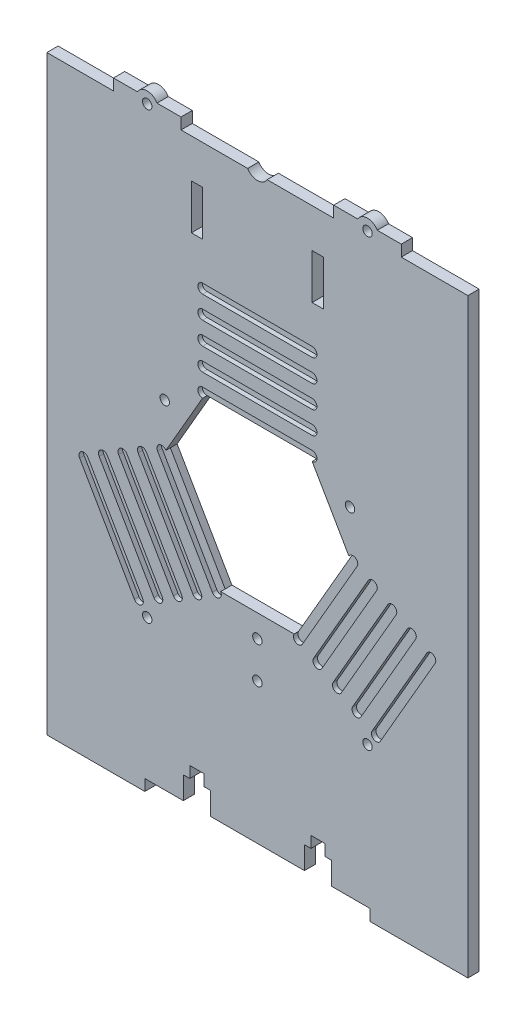
SolidWorks part; units mm, degrees
ref_plane "Front Plane" through (0, 0, 0) normal (0, 0, 1) x (1, 0, 0)
ref_plane "Top Plane" through (0, 0, 0) normal (0, 1, 0) x (1, 0, 0)
ref_plane "Right Plane" through (0, 0, 0) normal (1, 0, 0) x (0, 0, -1)
sketch "Sketch1" plane through (0, 0, 0) normal (0, 0, 1) x (1, 0, 0)
  line L1 (-93.5, 131.25) -> (93.5, 131.25)
  line L2 (-93.5, 131.25) -> (-93.5, -131.25)
  line L3 (-93.5, -131.25) -> (93.5, -131.25)
  line L4 (93.5, 131.25) -> (93.5, -131.25)
  line L5 (-93.5, 131.25) -> (93.5, -131.25) construction
  line L6 (-93.5, -131.25) -> (93.5, 131.25) construction
  point P0 (0, 0)
  dimension "D1" = 187
  dimension "D2" = 262.5
extrude "Boss-Extrude1" add sketch "Sketch1" along normal blind 5
sketch "Sketch2" plane through (0, 0, 5) normal (0, 0, 1) x (1, 0, 0)
  line L0 (-93.5, -131.25) -> (93.5, -131.25) construction
  line L1 (-50, -126.25) -> (50, -126.25)
  line L2 (-50, -126.25) -> (-50, -131.25)
  line L3 (-50, -131.25) -> (50, -131.25)
  line L4 (50, -126.25) -> (50, -131.25)
  line L5 (-50, -126.25) -> (50, -131.25) construction
  line L6 (-50, -131.25) -> (50, -126.25) construction
  line L7 (50, -126.25) -> (50, -131.25) construction
  circle A0 centre (0, 133.75) radius 5
  point P4 (0, -128.75)
extrude "Cut-Extrude1" cut sketch "Sketch2" against normal blind 5
sketch "Sketch4" plane through (0, 0, 5) normal (0, 0, 1) x (1, 0, 0)
  line L0 (48.9151, 131.25) -> (48.9151, 136.25) construction
  line L1 (93.5, 131.25) -> (4.3301, 131.25) construction
  line L2 (98, 136.25) -> (63.9151, 136.25) construction
  line L3 (0, 128.75) -> (0, 116.8054) construction
  line L4 (33.9151, 136.25) -> (44.5849, 136.25)
  line L5 (33.9151, 136.25) -> (33.9151, 131.25)
  line L6 (33.9151, 131.25) -> (63.9151, 131.25)
  line L7 (63.9151, 131.25) -> (63.9151, 136.25)
  line L8 (33.9151, 133.75) -> (63.9151, 133.75) construction
  line L9 (53.2452, 136.25) -> (63.9151, 136.25)
  line L10 (-33.9151, 133.75) -> (-63.9151, 133.75) construction
  line L11 (-48.9151, 131.25) -> (-48.9151, 136.25) construction
  line L12 (-53.2452, 136.25) -> (-63.9151, 136.25)
  line L13 (-63.9151, 131.25) -> (-63.9151, 136.25)
  line L14 (-33.9151, 131.25) -> (-63.9151, 131.25)
  line L15 (-33.9151, 136.25) -> (-33.9151, 131.25)
  line L16 (-33.9151, 136.25) -> (-44.5849, 136.25)
  arc A0 (-4.3301, 131.25) -> (4.3301, 131.25) centre (0, 133.75) ccw construction
  arc A1 (53.2452, 136.25) -> (44.5849, 136.25) centre (48.9151, 133.75) ccw
  arc A2 (-53.2452, 136.25) -> (-44.5849, 136.25) centre (-48.9151, 133.75) cw
  point P16 (48.9151, 136.25)
  point P34 (-48.9151, 136.25)
  dimension "D2" = 10
  dimension "D1" = 30
extrude "Boss-Extrude2" add sketch "Sketch4" against normal blind 5
sketch "Sketch3" plane through (0, 0, 5) normal (0, 0, 1) x (1, 0, 0)
  line L0 (0, -126.25) -> (0, -94.9289) construction
  line L1 (50, -126.25) -> (-50, -126.25) construction
  line L2 (0, -94.9289) -> (-53.8131, -94.9289) construction
  line L3 (-26.9066, -94.9289) -> (-26.9066, -126.25) construction
  line L4 (-32.9066, -126.25) -> (-32.9066, -116.25)
  line L5 (-32.9066, -116.25) -> (-30.0066, -116.25)
  line L6 (-30.0066, -116.25) -> (-30.0066, -111.25)
  line L7 (-23.8066, -116.25) -> (-23.8066, -111.25)
  line L8 (-20.9066, -116.25) -> (-23.8066, -116.25)
  line L9 (-20.9066, -126.25) -> (-20.9066, -116.25)
  line L10 (-30.0066, -111.25) -> (-23.8066, -111.25)
  line L11 (-32.9066, -126.25) -> (-20.9066, -126.25)
  line L12 (32.9066, -126.25) -> (20.9066, -126.25)
  line L13 (30.0066, -111.25) -> (23.8066, -111.25)
  line L14 (20.9066, -126.25) -> (20.9066, -116.25)
  line L15 (20.9066, -116.25) -> (23.8066, -116.25)
  line L16 (23.8066, -116.25) -> (23.8066, -111.25)
  line L17 (30.0066, -116.25) -> (30.0066, -111.25)
  line L18 (32.9066, -116.25) -> (30.0066, -116.25)
  line L19 (32.9066, -126.25) -> (32.9066, -116.25)
  line L20 (-63.9151, -63.75) -> (-33.9151, -63.75) construction
  line L21 (-63.9151, -61.25) -> (-63.9151, -66.25) construction
  line L22 (-33.9151, -61.25) -> (-33.9151, -66.25) construction
  line L23 (-15, -63.75) -> (15, -63.75) construction
  line L24 (-15, -61.25) -> (-15, -66.25) construction
  line L25 (15, -61.25) -> (15, -66.25) construction
  line L26 (33.9151, -63.75) -> (63.9151, -63.75) construction
  line L27 (33.9151, -61.25) -> (33.9151, -66.25) construction
  line L28 (63.9151, -61.25) -> (63.9151, -66.25) construction
  circle A0 centre (-48.9151, 133.75) radius 2.1
  circle A1 centre (48.9151, 133.75) radius 2.1
  circle A2 centre (-48.9151, -63.75) radius 2.1
  circle A3 centre (0, -63.75) radius 2.1
  circle A4 centre (48.9151, -63.75) radius 2.1
  dimension "D5" = 4.2
  dimension "D6" = 4.2
  dimension "D7" = 4.2
  dimension "D1" = 10
  dimension "D2" = 2.9
  dimension "D3" = 5
  dimension "D4" = 6
extrude "Cut-Extrude2" cut sketch "Sketch3" against normal blind 5
sketch "Sketch5" plane through (0, 0, 5) normal (0, 0, 1) x (1, 0, 0)
  line L0 (0, 0) -> (0, 75) construction
  line L1 (0, 0) -> (64.9519, -37.5) construction
  line L2 (0, 0) -> (-64.9519, -37.5) construction
  line L3 (-24.334, 75) -> (24.334, 75) construction
  line L4 (-24.334, 77.1191) -> (24.334, 77.1191)
  line L5 (-24.334, 72.8809) -> (24.334, 72.8809)
  line L6 (-24.334, 65) -> (24.334, 65) construction
  line L7 (-24.334, 67.1191) -> (24.334, 67.1191)
  line L8 (-24.334, 62.8809) -> (24.334, 62.8809)
  line L9 (-24.334, 55) -> (24.334, 55) construction
  line L10 (-24.334, 57.1191) -> (24.334, 57.1191)
  line L11 (-24.334, 52.8809) -> (24.334, 52.8809)
  line L12 (-24.334, 45) -> (24.334, 45) construction
  line L13 (-24.334, 47.1191) -> (24.334, 47.1191)
  line L14 (-24.334, 42.8809) -> (24.334, 42.8809)
  line L15 (-24.334, 35) -> (24.334, 35) construction
  line L16 (-24.334, 37.1191) -> (24.334, 37.1191)
  line L17 (-24.334, 32.8809) -> (24.334, 32.8809)
  line L18 (-24.334, 25) -> (24.334, 25) construction
  line L19 (-24.334, 27.1191) -> (24.334, 27.1191)
  line L20 (-24.334, 22.8809) -> (24.334, 22.8809)
  line L21 (77.1189, -16.4261) -> (52.7849, -58.5739) construction
  line L22 (78.9541, -17.4857) -> (54.6201, -59.6334)
  line L23 (75.2837, -15.3666) -> (50.9497, -57.5143)
  line L24 (68.4587, -11.4261) -> (44.1247, -53.5739) construction
  line L25 (70.2938, -12.4857) -> (45.9598, -54.6334)
  line L26 (66.6235, -10.3666) -> (42.2895, -52.5143)
  line L27 (59.7984, -6.4261) -> (35.4644, -48.5739) construction
  line L28 (61.6336, -7.4857) -> (37.2996, -49.6334)
  line L29 (57.9632, -5.3666) -> (33.6292, -47.5143)
  line L30 (51.1381, -1.4261) -> (26.8041, -43.5739) construction
  line L31 (52.9733, -2.4857) -> (28.6393, -44.6334)
  line L32 (49.303, -0.3666) -> (24.969, -42.5143)
  line L33 (42.4779, 3.5739) -> (18.1439, -38.5739) construction
  line L34 (44.3131, 2.5143) -> (19.9791, -39.6334)
  line L35 (40.6427, 4.6334) -> (16.3087, -37.5143)
  line L36 (33.8176, 8.5739) -> (9.4836, -33.5739) construction
  line L37 (35.6528, 7.5143) -> (11.3188, -34.6334)
  line L38 (31.9825, 9.6334) -> (7.6485, -32.5143)
  line L39 (-52.7849, -58.5739) -> (-77.1189, -16.4261) construction
  line L40 (-54.6201, -59.6334) -> (-78.9541, -17.4857)
  line L41 (-50.9497, -57.5143) -> (-75.2837, -15.3666)
  line L42 (-44.1247, -53.5739) -> (-68.4587, -11.4261) construction
  line L43 (-45.9598, -54.6334) -> (-70.2938, -12.4857)
  line L44 (-42.2895, -52.5143) -> (-66.6235, -10.3666)
  line L45 (-35.4644, -48.5739) -> (-59.7984, -6.4261) construction
  line L46 (-37.2996, -49.6334) -> (-61.6336, -7.4857)
  line L47 (-33.6292, -47.5143) -> (-57.9632, -5.3666)
  line L48 (-26.8041, -43.5739) -> (-51.1381, -1.4261) construction
  line L49 (-28.6393, -44.6334) -> (-52.9733, -2.4857)
  line L50 (-24.969, -42.5143) -> (-49.303, -0.3666)
  line L51 (-18.1439, -38.5739) -> (-42.4779, 3.5739) construction
  line L52 (-19.9791, -39.6334) -> (-44.3131, 2.5143)
  line L53 (-16.3087, -37.5143) -> (-40.6427, 4.6334)
  line L54 (-9.4836, -33.5739) -> (-33.8176, 8.5739) construction
  line L55 (-11.3188, -34.6334) -> (-35.6528, 7.5143)
  line L56 (-7.6485, -32.5143) -> (-31.9825, 9.6334)
  circle A0 centre (0, 0) radius 75 construction
  arc A1 (-24.334, 77.1191) -> (-24.334, 72.8809) centre (-24.334, 75) ccw
  arc A2 (24.334, 72.8809) -> (24.334, 77.1191) centre (24.334, 75) ccw
  arc A3 (-24.334, 67.1191) -> (-24.334, 62.8809) centre (-24.334, 65) ccw
  arc A4 (24.334, 62.8809) -> (24.334, 67.1191) centre (24.334, 65) ccw
  arc A5 (-24.334, 57.1191) -> (-24.334, 52.8809) centre (-24.334, 55) ccw
  arc A6 (24.334, 52.8809) -> (24.334, 57.1191) centre (24.334, 55) ccw
  arc A7 (-24.334, 47.1191) -> (-24.334, 42.8809) centre (-24.334, 45) ccw
  arc A8 (24.334, 42.8809) -> (24.334, 47.1191) centre (24.334, 45) ccw
  arc A9 (-24.334, 37.1191) -> (-24.334, 32.8809) centre (-24.334, 35) ccw
  arc A10 (24.334, 32.8809) -> (24.334, 37.1191) centre (24.334, 35) ccw
  arc A11 (-24.334, 27.1191) -> (-24.334, 22.8809) centre (-24.334, 25) ccw
  arc A12 (24.334, 22.8809) -> (24.334, 27.1191) centre (24.334, 25) ccw
  arc A13 (78.9541, -17.4857) -> (75.2837, -15.3666) centre (77.1189, -16.4261) ccw
  arc A14 (50.9497, -57.5143) -> (54.6201, -59.6334) centre (52.7849, -58.5739) ccw
  arc A15 (70.2938, -12.4857) -> (66.6235, -10.3666) centre (68.4587, -11.4261) ccw
  arc A16 (42.2895, -52.5143) -> (45.9598, -54.6334) centre (44.1247, -53.5739) ccw
  arc A17 (61.6336, -7.4857) -> (57.9632, -5.3666) centre (59.7984, -6.4261) ccw
  arc A18 (33.6292, -47.5143) -> (37.2996, -49.6334) centre (35.4644, -48.5739) ccw
  arc A19 (52.9733, -2.4857) -> (49.303, -0.3666) centre (51.1381, -1.4261) ccw
  arc A20 (24.969, -42.5143) -> (28.6393, -44.6334) centre (26.8041, -43.5739) ccw
  arc A21 (44.3131, 2.5143) -> (40.6427, 4.6334) centre (42.4779, 3.5739) ccw
  arc A22 (16.3087, -37.5143) -> (19.9791, -39.6334) centre (18.1439, -38.5739) ccw
  arc A23 (35.6528, 7.5143) -> (31.9825, 9.6334) centre (33.8176, 8.5739) ccw
  arc A24 (7.6485, -32.5143) -> (11.3188, -34.6334) centre (9.4836, -33.5739) ccw
  arc A25 (-54.6201, -59.6334) -> (-50.9497, -57.5143) centre (-52.7849, -58.5739) ccw
  arc A26 (-75.2837, -15.3666) -> (-78.9541, -17.4857) centre (-77.1189, -16.4261) ccw
  arc A27 (-45.9598, -54.6334) -> (-42.2895, -52.5143) centre (-44.1247, -53.5739) ccw
  arc A28 (-66.6235, -10.3666) -> (-70.2938, -12.4857) centre (-68.4587, -11.4261) ccw
  arc A29 (-37.2996, -49.6334) -> (-33.6292, -47.5143) centre (-35.4644, -48.5739) ccw
  arc A30 (-57.9632, -5.3666) -> (-61.6336, -7.4857) centre (-59.7984, -6.4261) ccw
  arc A31 (-28.6393, -44.6334) -> (-24.969, -42.5143) centre (-26.8041, -43.5739) ccw
  arc A32 (-49.303, -0.3666) -> (-52.9733, -2.4857) centre (-51.1381, -1.4261) ccw
  arc A33 (-19.9791, -39.6334) -> (-16.3087, -37.5143) centre (-18.1439, -38.5739) ccw
  arc A34 (-40.6427, 4.6334) -> (-44.3131, 2.5143) centre (-42.4779, 3.5739) ccw
  arc A35 (-11.3188, -34.6334) -> (-7.6485, -32.5143) centre (-9.4836, -33.5739) ccw
  arc A36 (-31.9825, 9.6334) -> (-35.6528, 7.5143) centre (-33.8176, 8.5739) ccw
  point P8 (0, 75)
  point P16 (0, 65)
  point P23 (0, 55)
  point P30 (0, 45)
  point P37 (0, 35)
  point P43 (0, 25)
  point P53 (64.9519, -37.5)
  point P61 (56.2917, -32.5)
  point P68 (47.6314, -27.5)
  point P75 (38.9711, -22.5)
  point P82 (30.3109, -17.5)
  point P88 (21.6506, -12.5)
  point P95 (-64.9519, -37.5)
  point P103 (-56.2917, -32.5)
  point P110 (-47.6314, -27.5)
  point P117 (-38.9711, -22.5)
  point P124 (-30.3109, -17.5)
  point P130 (-21.6506, -12.5)
  point P135 (0, 0)
  dimension "D1" = 150
  dimension "D2" = 120
  dimension "D3" = 120
  dimension "D4" = 6
  dimension "D5" = 3
extrude "Cut-Extrude3" cut sketch "Sketch5" against normal blind 2
sketch "Sketch6" plane through (0, 0, 5) normal (0, 0, 1) x (1, 0, 0)
  line L9 (-24.334, 32.8809) -> (24.334, 32.8809) construction
  line L10 (-16.3087, -37.5143) -> (-40.6427, 4.6334) construction
  line L11 (40.6427, 4.6334) -> (16.3087, -37.5143) construction
  line L12 (-24.334, 32.8809) -> (24.334, 32.8809)
  line L13 (-16.3087, -37.5143) -> (-40.6427, 4.6334)
  line L14 (40.6427, 4.6334) -> (16.3087, -37.5143)
  line L15 (40.6427, 4.6334) -> (24.334, 32.8809)
  line L16 (-24.334, 32.8809) -> (-40.6427, 4.6334)
  line L17 (16.3087, -37.5143) -> (-16.3087, -37.5143)
extrude "Cut-Extrude4" cut sketch "Sketch6" against normal through all
sketch "Sketch8" plane through (0, 0, 5) normal (0, 0, 1) x (1, 0, 0)
  line L0 (0, 128.75) -> (0, 115.8869) construction
  line L1 (-29.3067, 93.9791) -> (-24.3067, 93.9791)
  line L2 (-29.3067, 93.9791) -> (-29.3067, 113.9791)
  line L3 (-29.3067, 113.9791) -> (-24.3067, 113.9791)
  line L4 (-24.3067, 93.9791) -> (-24.3067, 113.9791)
  line L5 (-29.3067, 93.9791) -> (-24.3067, 113.9791) construction
  line L6 (-29.3067, 113.9791) -> (-24.3067, 93.9791) construction
  line L7 (29.3067, 113.9791) -> (24.3067, 93.9791) construction
  line L8 (29.3067, 93.9791) -> (24.3067, 113.9791) construction
  line L9 (24.3067, 93.9791) -> (24.3067, 113.9791)
  line L10 (29.3067, 113.9791) -> (24.3067, 113.9791)
  line L11 (29.3067, 93.9791) -> (29.3067, 113.9791)
  line L12 (29.3067, 93.9791) -> (24.3067, 93.9791)
  line L13 (0, -37.5143) -> (0, -47.5143) construction
  line L14 (-16.3087, -37.5143) -> (16.3087, -37.5143) construction
  arc A0 (-4.3301, 131.25) -> (4.3301, 131.25) centre (0, 133.75) ccw construction
  circle A1 centre (0, -47.5143) radius 2.1
  circle A2 centre (-41.1486, 23.7572) radius 2.1
  circle A3 centre (41.1486, 23.7572) radius 2.1
  point P4 (-26.8067, 103.9791)
  point P16 (26.8067, 103.9791)
  point P29 (0, 0)
  dimension "D4" = 4.2
  dimension "D1" = 20
  dimension "D2" = 5
  dimension "D3" = 10
  dimension "D5" = 3
extrude "Cut-Extrude5" cut sketch "Sketch8" against normal blind 10
